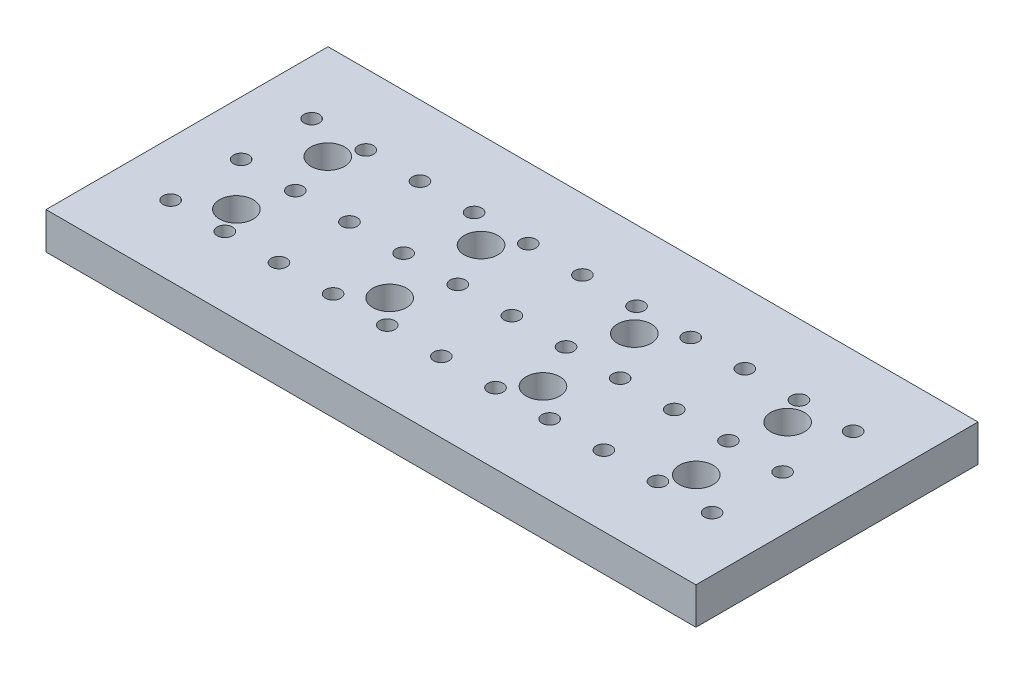
SolidWorks part; units mm, degrees
ref_plane "Front Plane" through (0, 0, 0) normal (0, 0, 1) x (1, 0, 0)
ref_plane "Top Plane" through (0, 0, 0) normal (0, 1, 0) x (1, 0, 0)
ref_plane "Right Plane" through (0, 0, 0) normal (1, 0, 0) x (0, 0, -1)
sketch "Sketch1" plane through (0, 0, 0) normal (0, 1, 0) x (1, 0, 0)
  line L1 (-72.2256, -12.0658) -> (33.7744, -12.0658)
  line L2 (-72.2256, -12.0658) -> (-72.2256, 33.9342)
  line L3 (-72.2256, 33.9342) -> (33.7744, 33.9342)
  line L4 (33.7744, -12.0658) -> (33.7744, 33.9342)
  dimension "D1" = 106
  dimension "D2" = 46
extrude "Boss-Extrude1" add sketch "Sketch1" against normal blind 6
hole_wizard "M5 Clearance Hole1" positions "3DSketch1" profile "Sketch2" hole size "M5" standard "ANSI Metric" end condition through all
sketch3d "3DSketch1"
  line L0 (-72.2256, 0, -33.9342) -> (-72.2256, 0, 12.0658) construction
  line L1 (33.7744, 0, -33.9342) -> (-72.2256, 0, -33.9342) construction
  line L2 (33.7744, 0, 12.0658) -> (33.7744, 0, -33.9342) construction
  line L3 (-72.2256, 0, 12.0658) -> (33.7744, 0, 12.0658) construction
  point P0 (-56.7256, 0, -18.3842)
  point P2 (-31.7256, 0, -18.3842)
  point P4 (-6.7256, 0, -18.3842)
  point P6 (18.2744, 0, -18.3842)
  point P8 (18.2744, 0, -3.4842)
  point P10 (-6.7256, 0, -3.4842)
  point P12 (-31.7256, 0, -3.4842)
  point P14 (-56.7256, 0, -3.4842)
  point P26 (0, 0, 0)
  dimension "D1" = 15.5
  dimension "D2" = 15.55
  dimension "D3" = 25
  dimension "D4" = 15.55
  dimension "D5" = 25
  dimension "D6" = 15.55
  dimension "D7" = 25
  dimension "D8" = 15.55
  dimension "D9" = 15.5
  dimension "D10" = 15.5
  dimension "D11" = 15.55
  dimension "D12" = 25
  dimension "D13" = 15.55
  dimension "D14" = 25
  dimension "D15" = 15.55
  dimension "D16" = 15.55
  dimension "D17" = 25
sketch "Sketch2" plane through (-56.7256, 0, -18.3842) normal (1, 0, 0) x (0, 0, 1)
  line L0 (0, 0) -> (0, 6)
  line L1 (0, 6) -> (2.75, 6)
  line L2 (2.75, 6) -> (2.75, 0)
  line L5 (2.75, 0) -> (0, 0)
  line L11 (0, -6.35) -> (0, 107.95) construction
  dimension "Thru Hole Dia." = 5.5
  dimension "Thru Hole Depth" = 6
hole_wizard "Tap Drill for M3x0.5 Tap1" positions "3DSketch2" profile "Sketch3" hole size "M3x0.5" standard "ANSI Metric" end condition through all
sketch3d "3DSketch2"
  line L0 (-72.2256, 0, 12.0658) -> (33.7744, 0, 12.0658) construction
  line L1 (-72.2256, 0, -33.9342) -> (-72.2256, 0, 12.0658) construction
  line L2 (33.7744, 0, -33.9342) -> (-72.2256, 0, -33.9342) construction
  point P0 (-63.3956, 0, 0.5658)
  point P2 (-54.5656, 0, 0.5658)
  point P4 (-36.9056, 0, 0.5658)
  point P6 (-28.0756, 0, 0.5658)
  point P8 (-10.4156, 0, 0.5658)
  point P10 (-19.2456, 0, 0.5658)
  point P12 (-45.7356, 0, 0.5658)
  point P14 (-1.5856, 0, 0.5658)
  point P16 (7.2444, 0, 0.5658)
  point P18 (16.0744, 0, 0.5658)
  point P20 (24.9044, 0, 0.5658)
  point P22 (24.9044, 0, -22.4342)
  point P24 (16.0744, 0, -22.4342)
  point P26 (7.2444, 0, -22.4342)
  point P28 (-1.5856, 0, -22.4342)
  point P30 (-10.4156, 0, -22.4342)
  point P32 (-19.2456, 0, -22.4342)
  point P34 (-28.0756, 0, -22.4342)
  point P36 (-36.9056, 0, -22.4342)
  point P38 (-45.7356, 0, -22.4342)
  point P40 (-54.5656, 0, -22.4342)
  point P42 (-63.3956, 0, -22.4342)
  point P44 (-63.3956, 0, -10.9342)
  point P46 (-54.5656, 0, -10.9342)
  point P48 (-45.7356, 0, -10.9342)
  point P50 (-36.9056, 0, -10.9342)
  point P52 (-10.4156, 0, -10.9342)
  point P54 (-1.5856, 0, -10.9342)
  point P56 (16.0744, 0, -10.9342)
  point P58 (24.9044, 0, -10.9342)
  point P68 (-28.0756, 0, -10.9342)
  point P70 (7.2444, 0, -10.9342)
  point P72 (-19.2456, 0, -10.9342)
  dimension "D1" = 11.5
  dimension "D2" = 8.83
  dimension "D3" = 8.83
  dimension "D4" = 11.5
  dimension "D5" = 8.83
  dimension "D6" = 11.5
  dimension "D7" = 11.5
  dimension "D8" = 8.83
  dimension "D9" = 8.83
  dimension "D10" = 11.5
  dimension "D11" = 8.83
  dimension "D12" = 11.5
  dimension "D13" = 8.83
  dimension "D14" = 11.5
  dimension "D15" = 8.83
  dimension "D16" = 11.5
  dimension "D17" = 8.83
  dimension "D18" = 11.5
  dimension "D19" = 8.83
  dimension "D20" = 11.5
  dimension "D21" = 8.83
  dimension "D22" = 11.5
  dimension "D23" = 8.83
  dimension "D24" = 11.5
  dimension "D25" = 8.83
  dimension "D26" = 11.5
  dimension "D27" = 8.83
  dimension "D28" = 11.5
  dimension "D29" = 8.83
  dimension "D30" = 11.5
  dimension "D31" = 8.83
  dimension "D32" = 11.5
  dimension "D33" = 8.83
  dimension "D34" = 11.5
  dimension "D35" = 8.83
  dimension "D36" = 11.5
  dimension "D37" = 8.83
  dimension "D38" = 11.5
  dimension "D39" = 8.83
  dimension "D40" = 11.5
  dimension "D41" = 8.83
  dimension "D42" = 11.5
  dimension "D43" = 8.83
  dimension "D44" = 11.5
  dimension "D45" = 8.83
  dimension "D46" = 11.5
  dimension "D47" = 8.83
  dimension "D48" = 11.5
  dimension "D49" = 8.83
  dimension "D50" = 11.5
  dimension "D51" = 8.83
  dimension "D52" = 11.5
  dimension "D53" = 8.83
  dimension "D54" = 11.5
  dimension "D55" = 8.83
  dimension "D56" = 11.5
  dimension "D57" = 8.83
  dimension "D58" = 11.5
  dimension "D59" = 8.83
  dimension "D60" = 11.5
  dimension "D61" = 8.83
  dimension "D62" = 11.5
  dimension "D63" = 8.83
  dimension "D64" = 11.5
  dimension "D65" = 8.83
  dimension "D66" = 11.5
sketch "Sketch3" plane through (-63.3956, 0, 0.5658) normal (1, 0, 0) x (0, 0, 1)
  line L0 (0, 0) -> (0, 6)
  line L1 (0, 6) -> (1.25, 6)
  line L2 (1.25, 6) -> (1.25, 0)
  line L5 (1.25, 0) -> (0, 0)
  line L11 (0, -6.35) -> (0, 107.95) construction
  dimension "Thru Hole Dia." = 2.5
  dimension "Thru Hole Depth" = 6
